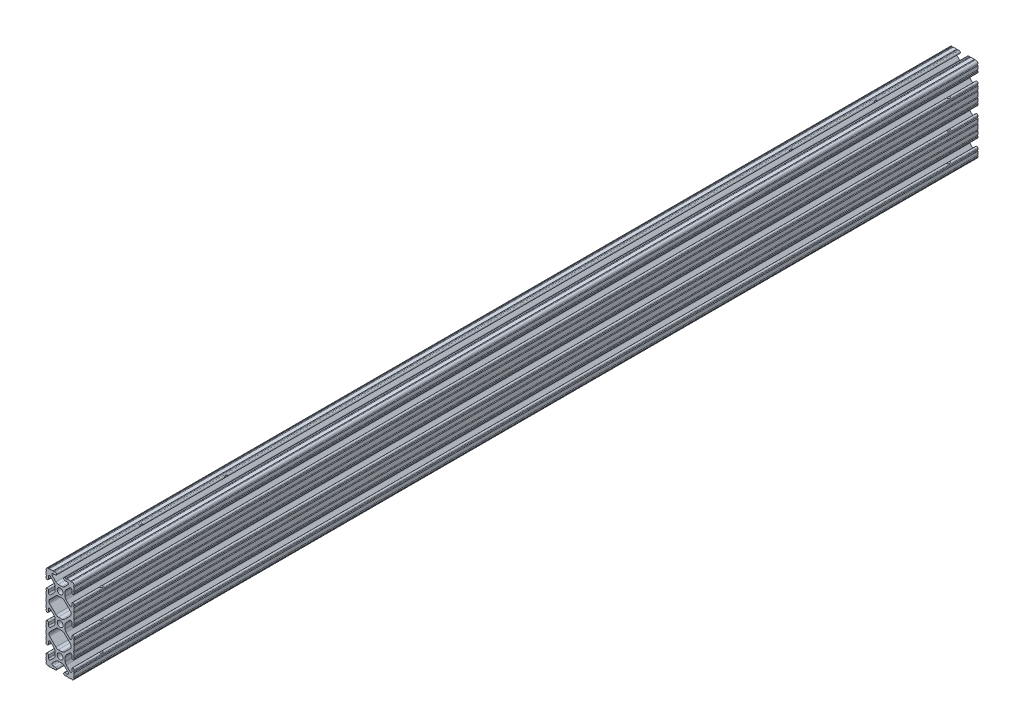
SolidWorks part; units mm, degrees
ref_plane "Front" through (0, 0, 0) normal (0, 0, 1) x (1, 0, 0)
ref_plane "Top" through (0, 0, 0) normal (0, 1, 0) x (1, 0, 0)
ref_plane "Right" through (0, 0, 0) normal (1, 0, 0) x (0, 0, -1)
sketch "Sketch1" plane through (0, 0, 0) normal (0, 0, 1) x (1, 0, 0)
  line L0 (-7.4908, -34.8742) -> (7.4908, -34.8742) construction
  line L1 (-3.1974, -36.9951) -> (3.1974, -36.9951) construction
  line L2 (-7.4908, 34.8742) -> (7.4908, 34.8742) construction
  line L3 (-3.1974, 36.9951) -> (3.1974, 36.9951) construction
  line L16 (-9.9314, -12.1463) -> (-9.9314, -13.2537)
  line L17 (-3.8759, -5.4384) -> (-9.4702, -11.0327)
  line L18 (1.6308, -4.5085) -> (-1.6308, -4.5085)
  line L19 (9.4702, -11.0327) -> (3.8759, -5.4384)
  line L20 (9.9314, -13.2537) -> (9.9314, -12.1463)
  line L21 (3.8759, -19.9616) -> (9.4702, -14.3673)
  line L22 (-1.6308, -20.8915) -> (1.6308, -20.8915)
  line L23 (-9.4702, -14.3673) -> (-3.8759, -19.9616)
  line L32 (-9.9314, 13.2537) -> (-9.9314, 12.1463)
  line L33 (-3.8759, 19.9616) -> (-9.4702, 14.3673)
  line L34 (1.6308, 20.8915) -> (-1.6308, 20.8915)
  line L35 (9.4702, 14.3673) -> (3.8759, 19.9616)
  line L36 (9.9314, 12.1463) -> (9.9314, 13.2537)
  line L37 (3.8759, 5.4384) -> (9.4702, 11.0327)
  line L38 (-1.6308, 4.5085) -> (1.6308, 4.5085)
  line L39 (-9.4702, 11.0327) -> (-3.8759, 5.4384)
  line L152 (-12.7, 34.9504) -> (-12.7, 31.7246)
  line L153 (-12.7, 30.7086) -> (-12.7, 29.7023)
  line L154 (-10.4902, 29.7023) -> (-10.4902, 31.8748)
  line L155 (-8.7558, 32.5932) -> (-5.4384, 29.2759)
  line L156 (-4.5085, 27.0308) -> (-4.5085, 23.7692)
  line L157 (-5.4384, 21.5241) -> (-8.7558, 18.2068)
  line L158 (-10.4902, 18.9252) -> (-10.4902, 21.0977)
  line L159 (-12.7, 21.0977) -> (-12.7, 20.0914)
  line L160 (-12.7, 19.0754) -> (-12.7, 15.8496)
  line L161 (-12.7, 14.8336) -> (-12.7, 10.5664)
  line L162 (-12.7, 9.5504) -> (-12.7, 6.3246)
  line L163 (-12.7, 5.3086) -> (-12.7, 4.3023)
  line L164 (-10.4902, 4.3023) -> (-10.4902, 6.4748)
  line L165 (-8.7558, 7.1932) -> (-5.4384, 3.8759)
  line L166 (-4.5085, 1.6308) -> (-4.5085, -1.6308)
  line L167 (-5.4384, -3.8759) -> (-8.7558, -7.1932)
  line L168 (-10.4902, -6.4748) -> (-10.4902, -4.3023)
  line L169 (-12.7, -4.3023) -> (-12.7, -5.3086)
  line L170 (-12.7, -6.3246) -> (-12.7, -9.5504)
  line L171 (-12.7, -10.5664) -> (-12.7, -14.8336)
  line L172 (-12.7, -15.8496) -> (-12.7, -19.0754)
  line L173 (-12.7, -20.0914) -> (-12.7, -21.0977)
  line L174 (-10.4902, -21.0977) -> (-10.4902, -18.9252)
  line L175 (-8.7558, -18.2068) -> (-5.4384, -21.5241)
  line L176 (-4.5085, -23.7692) -> (-4.5085, -27.0308)
  line L177 (-5.4384, -29.2759) -> (-8.7558, -32.5932)
  line L178 (-10.4902, -31.8748) -> (-10.4902, -29.7023)
  line L179 (-12.7, -29.7023) -> (-12.7, -30.7086)
  line L180 (-12.7, -31.7246) -> (-12.7, -34.9504)
  line L181 (-9.5504, -38.1) -> (-6.3246, -38.1)
  line L182 (-5.3086, -38.1) -> (-4.3023, -38.1)
  line L183 (-4.3023, -35.8902) -> (-6.4748, -35.8902)
  line L184 (-7.1932, -34.1558) -> (-3.8759, -30.8384)
  line L185 (-1.6308, -29.9085) -> (1.6308, -29.9085)
  line L186 (3.8759, -30.8384) -> (7.1932, -34.1558)
  line L187 (6.4748, -35.8902) -> (4.3023, -35.8902)
  line L188 (4.3023, -38.1) -> (5.3086, -38.1)
  line L189 (6.3246, -38.1) -> (9.5504, -38.1)
  line L190 (12.7, -34.9504) -> (12.7, -31.7246)
  line L191 (12.7, -30.7086) -> (12.7, -29.7023)
  line L192 (10.4902, -29.7023) -> (10.4902, -31.8748)
  line L193 (8.7558, -32.5932) -> (5.4384, -29.2759)
  line L194 (4.5085, -27.0308) -> (4.5085, -23.7692)
  line L195 (5.4384, -21.5241) -> (8.7558, -18.2068)
  line L196 (10.4902, -18.9252) -> (10.4902, -21.0977)
  line L197 (12.7, -21.0977) -> (12.7, -20.0914)
  line L198 (12.7, -19.0754) -> (12.7, -15.8496)
  line L199 (12.7, -14.8336) -> (12.7, -10.5664)
  line L200 (12.7, -9.5504) -> (12.7, -6.3246)
  line L201 (12.7, -5.3086) -> (12.7, -4.3023)
  line L202 (10.4902, -4.3023) -> (10.4902, -6.4748)
  line L203 (8.7558, -7.1932) -> (5.4384, -3.8759)
  line L204 (4.5085, -1.6308) -> (4.5085, 1.6308)
  line L205 (5.4384, 3.8759) -> (8.7558, 7.1932)
  line L206 (10.4902, 6.4748) -> (10.4902, 4.3023)
  line L207 (12.7, 4.3023) -> (12.7, 5.3086)
  line L208 (12.7, 6.3246) -> (12.7, 9.5504)
  line L209 (12.7, 10.5664) -> (12.7, 14.8336)
  line L210 (12.7, 15.8496) -> (12.7, 19.0754)
  line L211 (12.7, 20.0914) -> (12.7, 21.0977)
  line L212 (10.4902, 21.0977) -> (10.4902, 18.9252)
  line L213 (8.7558, 18.2068) -> (5.4384, 21.5241)
  line L214 (4.5085, 23.7692) -> (4.5085, 27.0308)
  line L215 (5.4384, 29.2759) -> (8.7558, 32.5932)
  line L216 (10.4902, 31.8748) -> (10.4902, 29.7023)
  line L217 (12.7, 29.7023) -> (12.7, 30.7086)
  line L218 (12.7, 31.7246) -> (12.7, 34.9504)
  line L219 (9.5504, 38.1) -> (6.3246, 38.1)
  line L220 (5.3086, 38.1) -> (4.3023, 38.1)
  line L221 (4.3023, 35.8902) -> (6.4748, 35.8902)
  line L222 (7.1932, 34.1558) -> (3.8759, 30.8384)
  line L223 (1.6308, 29.9085) -> (-1.6308, 29.9085)
  line L224 (-3.8759, 30.8384) -> (-7.1932, 34.1558)
  line L225 (-6.4748, 35.8902) -> (-4.3023, 35.8902)
  line L226 (-4.3023, 38.1) -> (-5.3086, 38.1)
  line L227 (-6.3246, 38.1) -> (-9.5504, 38.1)
  circle A2 centre (0, -25.4) radius 2.6035
  circle A4 centre (0, 0) radius 2.6035
  circle A6 centre (0, 25.4) radius 2.6035
  arc A18 (-9.9314, -13.2537) -> (-9.4702, -14.3673) centre (-8.3566, -13.2537) ccw
  arc A19 (-9.4702, -11.0327) -> (-9.9314, -12.1463) centre (-8.3566, -12.1463) ccw
  arc A20 (-1.6308, -4.5085) -> (-3.8759, -5.4384) centre (-1.6308, -7.6835) ccw
  arc A21 (3.8759, -5.4384) -> (1.6308, -4.5085) centre (1.6308, -7.6835) ccw
  arc A22 (9.9314, -12.1463) -> (9.4702, -11.0327) centre (8.3566, -12.1463) ccw
  arc A23 (9.4702, -14.3673) -> (9.9314, -13.2537) centre (8.3566, -13.2537) ccw
  arc A24 (1.6308, -20.8915) -> (3.8759, -19.9616) centre (1.6308, -17.7165) ccw
  arc A25 (-3.8759, -19.9616) -> (-1.6308, -20.8915) centre (-1.6308, -17.7165) ccw
  arc A36 (-9.9314, 12.1463) -> (-9.4702, 11.0327) centre (-8.3566, 12.1463) ccw
  arc A37 (-9.4702, 14.3673) -> (-9.9314, 13.2537) centre (-8.3566, 13.2537) ccw
  arc A38 (-1.6308, 20.8915) -> (-3.8759, 19.9616) centre (-1.6308, 17.7165) ccw
  arc A39 (3.8759, 19.9616) -> (1.6308, 20.8915) centre (1.6308, 17.7165) ccw
  arc A40 (9.9314, 13.2537) -> (9.4702, 14.3673) centre (8.3566, 13.2537) ccw
  arc A41 (9.4702, 11.0327) -> (9.9314, 12.1463) centre (8.3566, 12.1463) ccw
  arc A42 (1.6308, 4.5085) -> (3.8759, 5.4384) centre (1.6308, 7.6835) ccw
  arc A43 (-3.8759, 5.4384) -> (-1.6308, 4.5085) centre (-1.6308, 7.6835) ccw
  arc A168 (-10.5664, 38.1) -> (-12.7, 35.9664) centre (-10.592, 35.992) ccw
  arc A169 (-12.7, 34.9504) -> (-12.7, 35.9664) centre (-12.7, 35.4584) ccw
  arc A170 (-12.7, 30.7086) -> (-12.7, 31.7246) centre (-12.7, 31.2166) ccw
  arc A171 (-12.7, 29.7023) -> (-10.4902, 29.7023) centre (-11.5951, 29.7023) ccw
  arc A172 (-8.7558, 32.5932) -> (-10.4902, 31.8748) centre (-9.4742, 31.8748) ccw
  arc A173 (-4.5085, 27.0308) -> (-5.4384, 29.2759) centre (-7.6835, 27.0308) ccw
  arc A174 (-5.4384, 21.5241) -> (-4.5085, 23.7692) centre (-7.6835, 23.7692) ccw
  arc A175 (-10.4902, 18.9252) -> (-8.7558, 18.2068) centre (-9.4742, 18.9252) ccw
  arc A176 (-10.4902, 21.0977) -> (-12.7, 21.0977) centre (-11.5951, 21.0977) ccw
  arc A177 (-12.7, 19.0754) -> (-12.7, 20.0914) centre (-12.7, 19.5834) ccw
  arc A178 (-12.7, 14.8336) -> (-12.7, 15.8496) centre (-12.7, 15.3416) ccw
  arc A179 (-12.7, 9.5504) -> (-12.7, 10.5664) centre (-12.7, 10.0584) ccw
  arc A180 (-12.7, 5.3086) -> (-12.7, 6.3246) centre (-12.7, 5.8166) ccw
  arc A181 (-12.7, 4.3023) -> (-10.4902, 4.3023) centre (-11.5951, 4.3023) ccw
  arc A182 (-8.7558, 7.1932) -> (-10.4902, 6.4748) centre (-9.4742, 6.4748) ccw
  arc A183 (-4.5085, 1.6308) -> (-5.4384, 3.8759) centre (-7.6835, 1.6308) ccw
  arc A184 (-5.4384, -3.8759) -> (-4.5085, -1.6308) centre (-7.6835, -1.6308) ccw
  arc A185 (-10.4902, -6.4748) -> (-8.7558, -7.1932) centre (-9.4742, -6.4748) ccw
  arc A186 (-10.4902, -4.3023) -> (-12.7, -4.3023) centre (-11.5951, -4.3023) ccw
  arc A187 (-12.7, -6.3246) -> (-12.7, -5.3086) centre (-12.7, -5.8166) ccw
  arc A188 (-12.7, -10.5664) -> (-12.7, -9.5504) centre (-12.7, -10.0584) ccw
  arc A189 (-12.7, -15.8496) -> (-12.7, -14.8336) centre (-12.7, -15.3416) ccw
  arc A190 (-12.7, -20.0914) -> (-12.7, -19.0754) centre (-12.7, -19.5834) ccw
  arc A191 (-12.7, -21.0977) -> (-10.4902, -21.0977) centre (-11.5951, -21.0977) ccw
  arc A192 (-8.7558, -18.2068) -> (-10.4902, -18.9252) centre (-9.4742, -18.9252) ccw
  arc A193 (-4.5085, -23.7692) -> (-5.4384, -21.5241) centre (-7.6835, -23.7692) ccw
  arc A194 (-5.4384, -29.2759) -> (-4.5085, -27.0308) centre (-7.6835, -27.0308) ccw
  arc A195 (-10.4902, -31.8748) -> (-8.7558, -32.5932) centre (-9.4742, -31.8748) ccw
  arc A196 (-10.4902, -29.7023) -> (-12.7, -29.7023) centre (-11.5951, -29.7023) ccw
  arc A197 (-12.7, -31.7246) -> (-12.7, -30.7086) centre (-12.7, -31.2166) ccw
  arc A198 (-12.7, -35.9664) -> (-12.7, -34.9504) centre (-12.7, -35.4584) ccw
  arc A199 (-12.7, -35.9664) -> (-10.5664, -38.1) centre (-10.592, -35.992) ccw
  arc A200 (-9.5504, -38.1) -> (-10.5664, -38.1) centre (-10.0584, -38.1) ccw
  arc A201 (-5.3086, -38.1) -> (-6.3246, -38.1) centre (-5.8166, -38.1) ccw
  arc A202 (-4.3023, -38.1) -> (-4.3023, -35.8902) centre (-4.3023, -36.9951) ccw
  arc A203 (-7.1932, -34.1558) -> (-6.4748, -35.8902) centre (-6.4748, -34.8742) ccw
  arc A204 (-1.6308, -29.9085) -> (-3.8759, -30.8384) centre (-1.6308, -33.0835) ccw
  arc A205 (3.8759, -30.8384) -> (1.6308, -29.9085) centre (1.6308, -33.0835) ccw
  arc A206 (6.4748, -35.8902) -> (7.1932, -34.1558) centre (6.4748, -34.8742) ccw
  arc A207 (4.3023, -35.8902) -> (4.3023, -38.1) centre (4.3023, -36.9951) ccw
  arc A208 (6.3246, -38.1) -> (5.3086, -38.1) centre (5.8166, -38.1) ccw
  arc A209 (10.5664, -38.1) -> (9.5504, -38.1) centre (10.0584, -38.1) ccw
  arc A210 (10.5664, -38.1) -> (12.7, -35.9664) centre (10.592, -35.992) ccw
  arc A211 (12.7, -34.9504) -> (12.7, -35.9664) centre (12.7, -35.4584) ccw
  arc A212 (12.7, -30.7086) -> (12.7, -31.7246) centre (12.7, -31.2166) ccw
  arc A213 (12.7, -29.7023) -> (10.4902, -29.7023) centre (11.5951, -29.7023) ccw
  arc A214 (8.7558, -32.5932) -> (10.4902, -31.8748) centre (9.4742, -31.8748) ccw
  arc A215 (4.5085, -27.0308) -> (5.4384, -29.2759) centre (7.6835, -27.0308) ccw
  arc A216 (5.4384, -21.5241) -> (4.5085, -23.7692) centre (7.6835, -23.7692) ccw
  arc A217 (10.4902, -18.9252) -> (8.7558, -18.2068) centre (9.4742, -18.9252) ccw
  arc A218 (10.4902, -21.0977) -> (12.7, -21.0977) centre (11.5951, -21.0977) ccw
  arc A219 (12.7, -19.0754) -> (12.7, -20.0914) centre (12.7, -19.5834) ccw
  arc A220 (12.7, -14.8336) -> (12.7, -15.8496) centre (12.7, -15.3416) ccw
  arc A221 (12.7, -9.5504) -> (12.7, -10.5664) centre (12.7, -10.0584) ccw
  arc A222 (12.7, -5.3086) -> (12.7, -6.3246) centre (12.7, -5.8166) ccw
  arc A223 (12.7, -4.3023) -> (10.4902, -4.3023) centre (11.5951, -4.3023) ccw
  arc A224 (8.7558, -7.1932) -> (10.4902, -6.4748) centre (9.4742, -6.4748) ccw
  arc A225 (4.5085, -1.6308) -> (5.4384, -3.8759) centre (7.6835, -1.6308) ccw
  arc A226 (5.4384, 3.8759) -> (4.5085, 1.6308) centre (7.6835, 1.6308) ccw
  arc A227 (10.4902, 6.4748) -> (8.7558, 7.1932) centre (9.4742, 6.4748) ccw
  arc A228 (10.4902, 4.3023) -> (12.7, 4.3023) centre (11.5951, 4.3023) ccw
  arc A229 (12.7, 6.3246) -> (12.7, 5.3086) centre (12.7, 5.8166) ccw
  arc A230 (12.7, 10.5664) -> (12.7, 9.5504) centre (12.7, 10.0584) ccw
  arc A231 (12.7, 15.8496) -> (12.7, 14.8336) centre (12.7, 15.3416) ccw
  arc A232 (12.7, 20.0914) -> (12.7, 19.0754) centre (12.7, 19.5834) ccw
  arc A233 (12.7, 21.0977) -> (10.4902, 21.0977) centre (11.5951, 21.0977) ccw
  arc A234 (8.7558, 18.2068) -> (10.4902, 18.9252) centre (9.4742, 18.9252) ccw
  arc A235 (4.5085, 23.7692) -> (5.4384, 21.5241) centre (7.6835, 23.7692) ccw
  arc A236 (5.4384, 29.2759) -> (4.5085, 27.0308) centre (7.6835, 27.0308) ccw
  arc A237 (10.4902, 31.8748) -> (8.7558, 32.5932) centre (9.4742, 31.8748) ccw
  arc A238 (10.4902, 29.7023) -> (12.7, 29.7023) centre (11.5951, 29.7023) ccw
  arc A239 (12.7, 31.7246) -> (12.7, 30.7086) centre (12.7, 31.2166) ccw
  arc A240 (12.7, 35.9664) -> (12.7, 34.9504) centre (12.7, 35.4584) ccw
  arc A241 (12.7, 35.9664) -> (10.5664, 38.1) centre (10.592, 35.992) ccw
  arc A242 (9.5504, 38.1) -> (10.5664, 38.1) centre (10.0584, 38.1) ccw
  arc A243 (5.3086, 38.1) -> (6.3246, 38.1) centre (5.8166, 38.1) ccw
  arc A244 (4.3023, 38.1) -> (4.3023, 35.8902) centre (4.3023, 36.9951) ccw
  arc A245 (7.1932, 34.1558) -> (6.4748, 35.8902) centre (6.4748, 34.8742) ccw
  arc A246 (1.6308, 29.9085) -> (3.8759, 30.8384) centre (1.6308, 33.0835) ccw
  arc A247 (-3.8759, 30.8384) -> (-1.6308, 29.9085) centre (-1.6308, 33.0835) ccw
  arc A248 (-6.4748, 35.8902) -> (-7.1932, 34.1558) centre (-6.4748, 34.8742) ccw
  arc A249 (-4.3023, 35.8902) -> (-4.3023, 38.1) centre (-4.3023, 36.9951) ccw
  arc A250 (-6.3246, 38.1) -> (-5.3086, 38.1) centre (-5.8166, 38.1) ccw
  arc A251 (-10.5664, 38.1) -> (-9.5504, 38.1) centre (-10.0584, 38.1) ccw
extrude "Boss-Extrude1" add sketch "Sketch1" along normal mid plane 812.8
sketch "Sketch2" plane through (4.5085, 0, 0) normal (1, 0, 0) x (0, 0, -1)
  line L0 (-406.4, 38.1) -> (406.4, 38.1) construction
  line L1 (-406.4, 23.7692) -> (-406.4, 27.0308) construction
  line L2 (-406.4, -1.6308) -> (-406.4, 1.6308) construction
  line L3 (-406.4, -27.0308) -> (-406.4, -23.7692) construction
  line L4 (0, 0) -> (0, 56.395) construction
  circle A0 centre (-381, 25.4) radius 3.5
  circle A1 centre (-381, 0) radius 3.5
  circle A2 centre (-381, -25.4) radius 3.5
  circle A3 centre (381, 25.4) radius 3.5
  circle A4 centre (381, 0) radius 3.5
  circle A5 centre (381, -25.4) radius 3.5
  dimension "D1" = 7
  dimension "D2" = 12.7
  dimension "D3" = 25.4
  dimension "D4" = 7
  dimension "D5" = 7
  dimension "D6" = 25.4
  dimension "D7" = 25.4
  dimension "D8" = 25.4
  dimension "D9" = 25.4
extrude "Cut-Extrude1" cut sketch "Sketch2" against normal through all both and the other way through all
sketch "Sketch4" plane through (0, -29.9085, 0) normal (0, -1, 0) x (1, 0, 0)
  line L0 (0, 0) -> (131.3157, 0) construction
  line L1 (-1.6308, 406.4) -> (1.6308, 406.4) construction
  circle A0 centre (0, 330.2) radius 3.5
  circle A1 centre (0, -330.2) radius 3.5
  circle A2 centre (0, 254) radius 3.5
  circle A3 centre (0, -254) radius 3.5
  dimension "D1" = 7
  dimension "D2" = 76.2
  dimension "D3" = 7
  dimension "D4" = 76.2
extrude "Cut-Extrude3" cut sketch "Sketch4" against normal through all both and the other way through all
